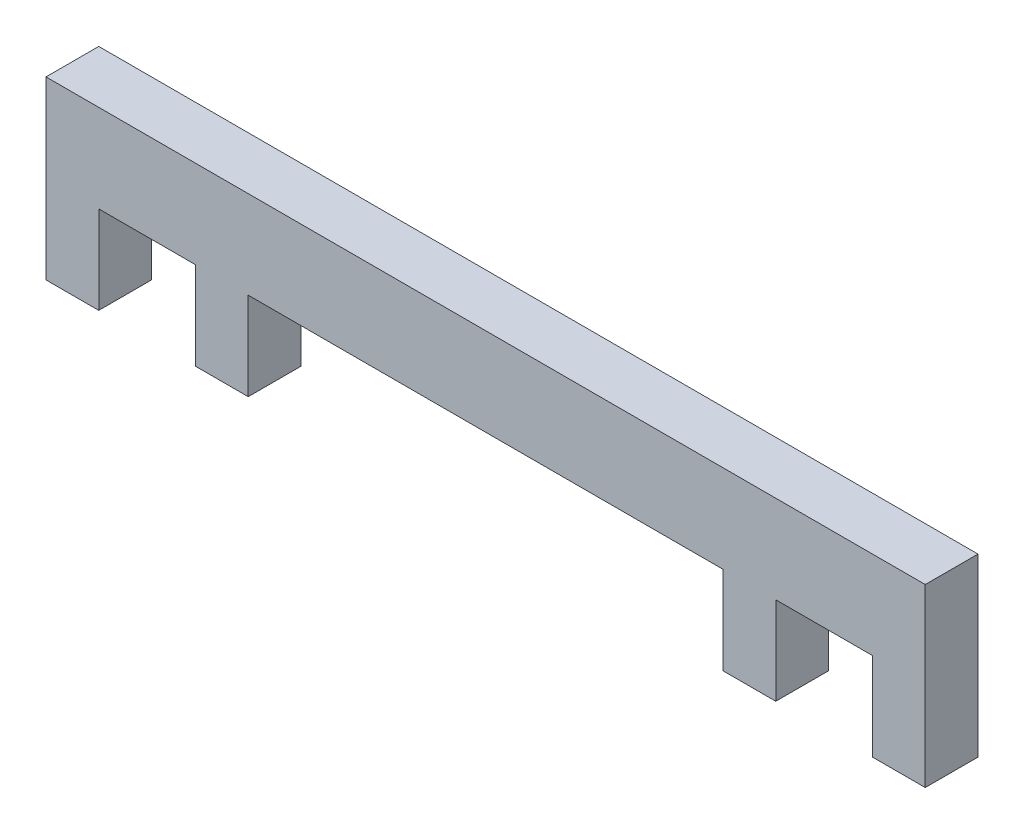
SolidWorks part; units mm, degrees
material "ﾁｰｸ材"
ref_plane "正面" through (0, 0, 0) normal (0, 0, 1) x (1, 0, 0)
ref_plane "平面" through (0, 0, 0) normal (0, 1, 0) x (1, 0, 0)
ref_plane "右側面" through (0, 0, 0) normal (1, 0, 0) x (0, 0, -1)
sketch "ｽｹｯﾁ1" plane through (0, 0, 0) normal (0, 0, 1) x (1, 0, 0)
  line L0 (0, 0) -> (-3, 0)
  line L1 (-3, 0) -> (-3, 10)
  line L2 (-3, 10) -> (47, 10)
  line L3 (47, 10) -> (47, 0)
  line L4 (47, 0) -> (44, 0)
  line L5 (44, 0) -> (44, 5)
  line L6 (44, 5) -> (38.5, 5)
  line L7 (38.5, 5) -> (38.5, 0)
  line L8 (38.5, 0) -> (35.5, 0)
  line L9 (35.5, 0) -> (35.5, 5)
  line L10 (35.5, 5) -> (8.5, 5)
  line L11 (8.5, 5) -> (8.5, 0)
  line L12 (8.5, 0) -> (5.5, 0)
  line L13 (5.5, 0) -> (5.5, 5)
  line L14 (5.5, 5) -> (0, 5)
  line L15 (0, 5) -> (0, 0)
  dimension "D1" = 3
  dimension "D2" = 5.5
  dimension "D3" = 44
  dimension "D4" = 3
  dimension "D5" = 3
  dimension "D6" = 3
  dimension "D7" = 5.5
  dimension "D8" = 5
  dimension "D9" = 5
extrude "ﾎﾞｽ - 押し出し1" add sketch "ｽｹｯﾁ1" along normal blind 3
